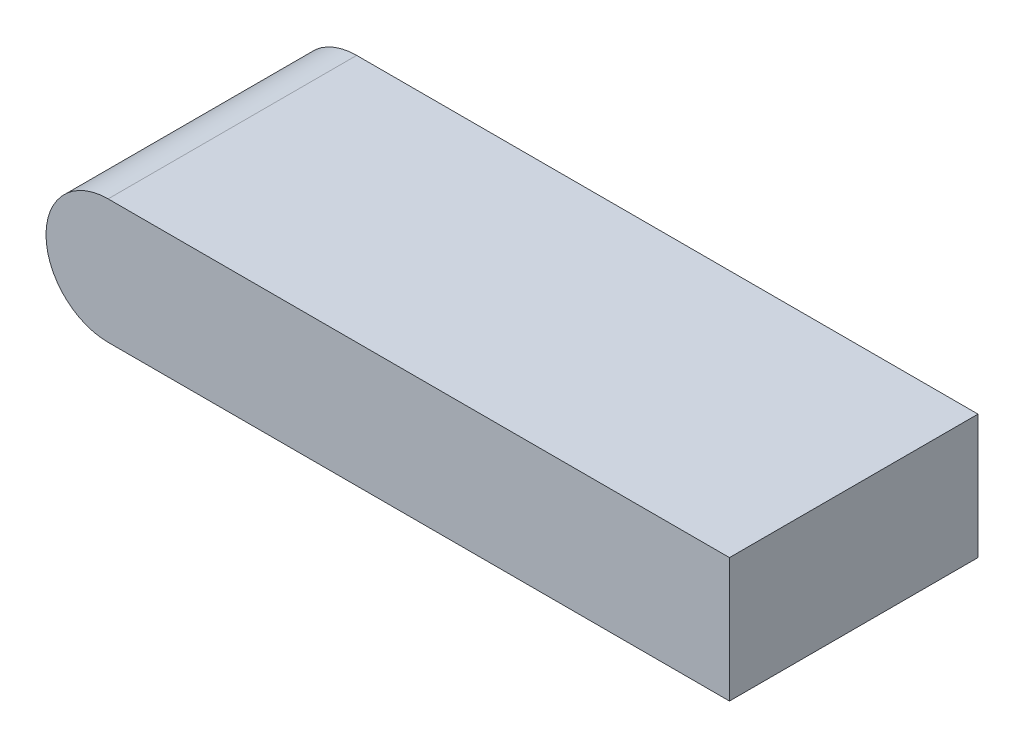
SolidWorks part; units mm, degrees
ref_plane "Front" through (0, 0, 0) normal (0, 0, 1) x (1, 0, 0)
ref_plane "Top" through (0, 0, 0) normal (0, 1, 0) x (1, 0, 0)
ref_plane "Right" through (0, 0, 0) normal (1, 0, 0) x (0, 0, -1)
sketch "草图1" plane through (0, 0, 0) normal (0, 1, 0) x (1, 0, 0)
  line L1 (-10, 4) -> (10, 4)
  line L2 (-10, 4) -> (-10, -4)
  line L3 (-10, -4) -> (10, -4)
  line L4 (10, 4) -> (10, -4)
  dimension "D1" = 8
  dimension "D2" = 20
  dimension "D3" = 10
  dimension "D4" = 4
extrude "凸台-拉伸1" add sketch "草图1" along normal blind 4
sketch "草图2" plane through (0, 0, 4) normal (0, 0, 1) x (1, 0, 0)
  line L0 (-10, 4) -> (-10, 0) construction
  circle A0 centre (-10, 2) radius 2
extrude "凸台-拉伸2" add sketch "草图2" against normal blind 8
